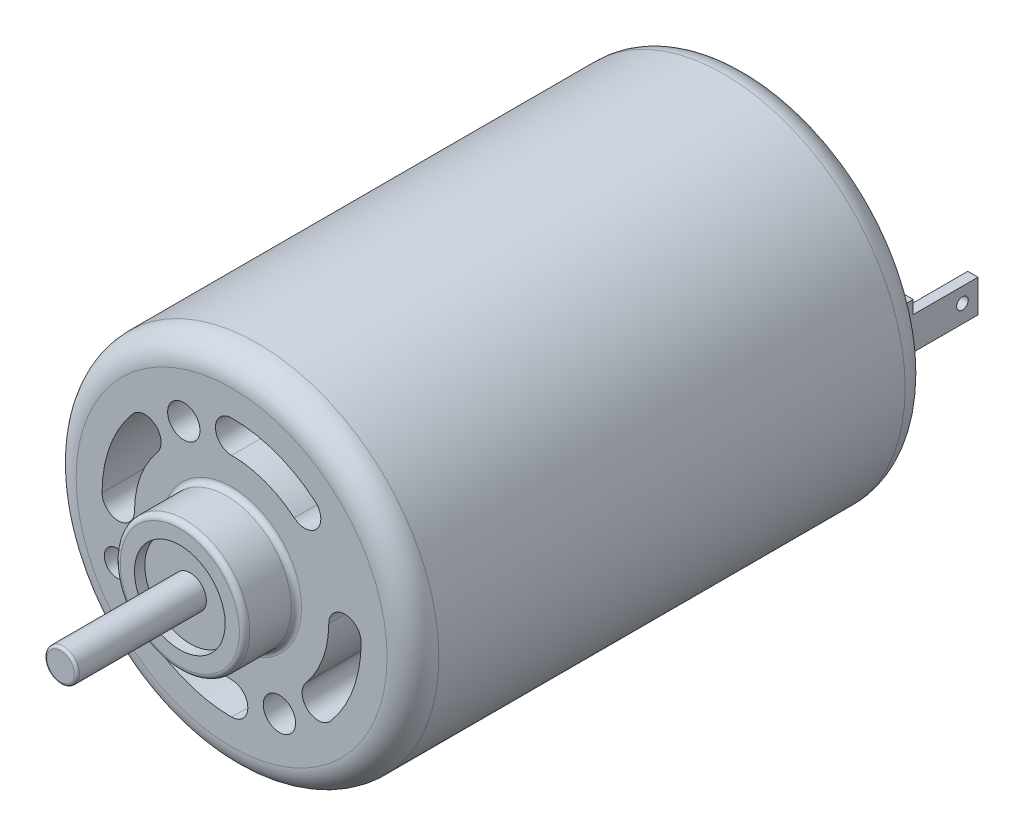
SolidWorks part; units mm, degrees
ref_plane "Front Plane" through (0, 0, 0) normal (0, 0, 1) x (1, 0, 0)
ref_plane "Top Plane" through (0, 0, 0) normal (0, 1, 0) x (1, 0, 0)
ref_plane "Right Plane" through (0, 0, 0) normal (1, 0, 0) x (0, 0, -1)
sketch "Sketch1" plane through (0, 0, 0) normal (0, 0, 1) x (1, 0, 0)
  circle A0 centre (0, 0) radius 17.78
  dimension "D1" = 35.56
extrude "Boss-Extrude1" add sketch "Sketch1" along normal blind 50.8
sketch "Sketch2" plane through (0, 0, 50.8) normal (0, 0, 1) x (1, 0, 0)
  circle A0 centre (0, 0) radius 6.35
  dimension "D1" = 12.7
extrude "Boss-Extrude2" add sketch "Sketch2" along normal blind 5.08
fillet "Fillet1" radius 0.508 2 edges at (6.35, 0, 50.8) (6.35, 0, 55.88)
sketch "Sketch3" plane through (0, 0, 55.88) normal (0, 0, 1) x (1, 0, 0)
  circle A0 centre (0, 0) radius 4.445
  dimension "D1" = 8.89
extrude "Cut-Extrude1" cut sketch "Sketch3" against normal blind 1.016
fillet "Fillet2" radius 2.54 2 edges at (17.78, 0, 0) (17.78, 0, 50.8)
sketch "Sketch4" plane through (0, 0, 0) normal (0, 0, -1) x (-1, 0, 0)
  circle A0 centre (0, 0) radius 6.35
  dimension "D1" = 12.7
extrude "Boss-Extrude3" add sketch "Sketch4" along normal blind 2.54 separate body
fillet "Fillet3" radius 1.27 1 edges at (-6.35, 0, -2.54)
sketch "Sketch5" plane through (0, 0, -2.54) normal (0, 0, -1) x (-1, 0, 0)
  circle A0 centre (0, 0) radius 1.5875
  dimension ".125" = 3.175
extrude "Boss-Extrude4" add sketch "Sketch5" along normal blind 1.524
fillet "Fillet4" radius 0.254 1 edges at (-1.5875, 0, -4.064)
sketch "Sketch6" plane through (0, 0, 54.864) normal (0, 0, 1) x (1, 0, 0)
  circle A0 centre (0, 0) radius 1.5875
  dimension "D1" = 3.175
extrude "Boss-Extrude5" add sketch "Sketch6" along normal blind 12.7
fillet "Fillet5" radius 0.254 1 edges at (1.5875, 0, 67.564)
sketch "Sketch7" plane through (0, 0, 50.8) normal (0, 0, 1) x (1, 0, 0)
  line L0 (0, 0) -> (8.1078, 22.2145) construction
  line L1 (0, 0) -> (22.2145, -8.1078) construction
  line L2 (0, 0) -> (-8.1078, -22.2145) construction
  line L3 (0, 0) -> (-22.2145, 8.1078) construction
  line L4 (0, 0) -> (-9.0284, 19.4067) construction
  line L5 (0, 0) -> (9.0284, -19.4067) construction
  arc A0 (8.1807, 9.7142) -> (0, 12.7) centre (0, 0) ccw
  arc A1 (6.1355, 7.2857) -> (0, 9.525) centre (0, 0) ccw
  circle A2 centre (0, 0) radius 11.1125 construction
  arc A3 (0, 12.7) -> (0, 9.525) centre (0, 11.1125) ccw
  arc A4 (8.1807, 9.7142) -> (6.1355, 7.2857) centre (7.1581, 8.4999) cw
  arc A5 (12.7, 0) -> (9.525, 0) centre (11.1125, 0) ccw
  arc A6 (9.7142, -8.1807) -> (7.2857, -6.1355) centre (8.4999, -7.1581) cw
  arc A7 (0, -12.7) -> (0, -9.525) centre (0, -11.1125) ccw
  arc A8 (-8.1807, -9.7142) -> (-6.1355, -7.2857) centre (-7.1581, -8.4999) cw
  arc A9 (-12.7, 0) -> (-9.525, 0) centre (-11.1125, 0) ccw
  arc A10 (-9.7142, 8.1807) -> (-7.2857, 6.1355) centre (-8.4999, 7.1581) cw
  arc A11 (-9.7142, 8.1807) -> (-12.7, 0) centre (0, 0) ccw
  arc A12 (-7.2857, 6.1355) -> (-9.525, 0) centre (0, 0) ccw
  arc A13 (-8.1807, -9.7142) -> (0, -12.7) centre (0, 0) ccw
  arc A14 (-6.1355, -7.2857) -> (0, -9.525) centre (0, 0) ccw
  arc A15 (7.2857, -6.1355) -> (9.525, 0) centre (0, 0) ccw
  arc A16 (9.7142, -8.1807) -> (12.7, 0) centre (0, 0) ccw
  circle A17 centre (-4.6874, 10.0755) radius 1.5875
  circle A18 centre (-11.2189, -5.2406) radius 1.27
  circle A19 centre (4.6874, -10.0755) radius 1.5875
  point P36 (0, 0)
  point P41 (0, 0)
  dimension "D1" = 19.05
  dimension "D2" = 25.4
  dimension "D3" = 22.225
  dimension "D4" = 1.5875
  dimension "D9" = 3.175
  dimension "D11" = 2.54
  dimension "D5" = 3.81
  dimension "D7" = 45
  dimension "D8" = 0
  dimension "D12" = 5.207
  dimension "D6" = 4
  dimension "D10" = 2
extrude "Cut-Extrude2" cut sketch "Sketch7" against normal blind 25.4
sketch "Sketch8" plane through (0, 0, 0) normal (0, 0, -1) x (-1, 0, 0)
  line L0 (1.5033, 0.5566) -> (24.29, 0.5566) construction
  line L1 (0, 0) -> (0, 3.3245) construction
  line L2 (14.1287, -2.3644) -> (11.2712, -2.3644)
  line L3 (14.1287, -2.3644) -> (14.1287, 3.4776)
  line L4 (14.1287, 3.4776) -> (11.2712, 3.4776)
  line L5 (11.2712, -2.3644) -> (11.2712, 3.4776)
  line L6 (14.1287, -2.3644) -> (11.2712, 3.4776) construction
  line L7 (14.1287, 3.4776) -> (11.2712, -2.3644) construction
  line L8 (-14.1287, 3.4776) -> (-11.2712, -2.3644) construction
  line L9 (-14.1287, -2.3644) -> (-11.2712, 3.4776) construction
  line L10 (-11.2712, -2.3644) -> (-11.2712, 3.4776)
  line L11 (-14.1287, 3.4776) -> (-11.2712, 3.4776)
  line L12 (-14.1287, -2.3644) -> (-14.1287, 3.4776)
  line L13 (-14.1287, -2.3644) -> (-11.2712, -2.3644)
  point P1 (12.7, 0.5566)
  point P15 (-12.7, 0.5566)
  dimension "D1" = 2.8575
  dimension ".5" = 12.7
  dimension "." = 5.842
extrude "Boss-Extrude6" add sketch "Sketch8" along normal blind 1.905
sketch "Sketch9" plane through (0, 0, -1.905) normal (0, 0, -1) x (-1, 0, 0)
  line L0 (0, 0) -> (0, 24.0407) construction
  line L1 (14.1287, -2.3644) -> (14.1287, 3.4776) construction
  line L2 (13.1298, 2.1912) -> (14.1287, 2.1912)
  line L3 (13.1298, 2.1912) -> (13.1298, -1.0133)
  line L4 (13.1298, -1.0133) -> (14.1287, -1.0133)
  line L5 (14.1287, 2.1912) -> (14.1287, -1.0133)
  line L6 (-14.1287, 2.1912) -> (-14.1287, -1.0133)
  line L7 (-13.1298, -1.0133) -> (-14.1287, -1.0133)
  line L8 (-13.1298, 2.1912) -> (-13.1298, -1.0133)
  line L9 (-13.1298, 2.1912) -> (-14.1287, 2.1912)
  dimension "D1" = 3.2045
  dimension "D2" = 0.999
extrude "Boss-Extrude7" add sketch "Sketch9" along normal blind 6.35
sketch "Sketch10" plane through (14.1287, 0, 0) normal (1, 0, 0) x (0, 0, -1)
  line L0 (8.255, 2.1912) -> (8.255, -1.0133) construction
  line L1 (8.255, 2.1912) -> (1.905, 2.1912) construction
  circle A0 centre (6.731, 0.7307) radius 0.5696
  dimension "D2" = 1.1391
  dimension "." = 1.524
  dimension "D1" = 1.4605
extrude "Cut-Extrude3" cut sketch "Sketch10" against normal through all
equation "\"D3@Sketch7\"=(1+.75)/2"
equation "\"D1@Sketch10\"=.23/4"
